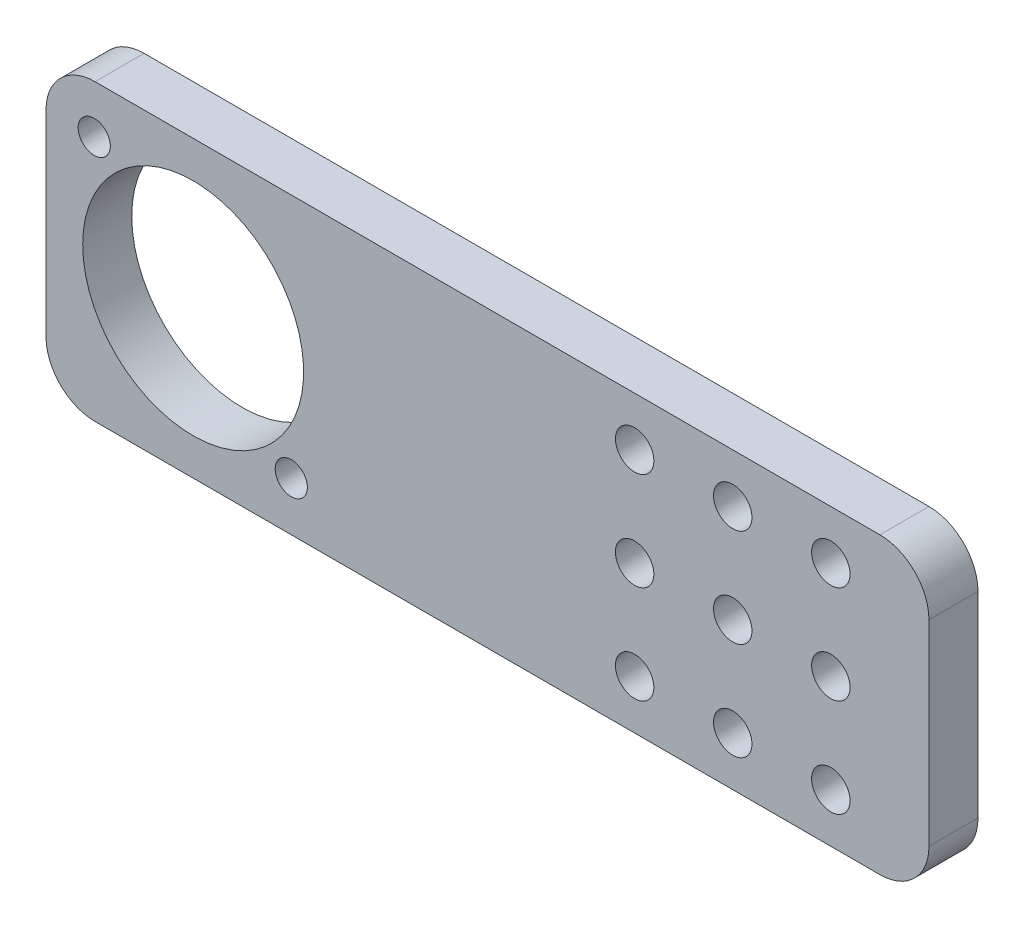
SolidWorks part; units mm, degrees
ref_plane "Front Plane" through (0, 0, 0) normal (0, 0, 1) x (1, 0, 0)
ref_plane "Top Plane" through (0, 0, 0) normal (0, 1, 0) x (1, 0, 0)
ref_plane "Right Plane" through (0, 0, 0) normal (1, 0, 0) x (0, 0, -1)
sketch "Sketch1" plane through (0, 0, 0) normal (0, 0, 1) x (1, 0, 0)
  line L0 (114.3, -12.7) -> (114.3, 12.7)
  line L1 (107.95, 19.05) -> (6.35, 19.05)
  line L2 (0, 12.7) -> (0, -12.7)
  line L3 (6.35, -19.05) -> (107.95, -19.05)
  line L4 (31.75, -12.7) -> (6.35, 12.7) construction
  circle A0 centre (19.05, 0) radius 14.3002
  circle A1 centre (6.2442, 12.8058) radius 2.0828
  circle A2 centre (31.75, -12.7) radius 2.0828
  circle A3 centre (88.9, 12.7) radius 2.4892
  circle A4 centre (101.6, 12.7) radius 2.4892
  circle A5 centre (88.9, 0) radius 2.4892
  circle A6 centre (101.6, 0) radius 2.4892
  circle A7 centre (88.9, -12.7) radius 2.4892
  circle A8 centre (76.2, 12.7) radius 2.4892
  circle A9 centre (101.6, -12.7) radius 2.4892
  circle A10 centre (76.2, 0) radius 2.4892
  circle A11 centre (76.2, -12.7) radius 2.4892
  arc A12 (107.95, -19.05) -> (114.3, -12.7) centre (107.95, -12.7) ccw
  arc A13 (114.3, 12.7) -> (107.95, 19.05) centre (107.95, 12.7) ccw
  arc A14 (6.35, 19.05) -> (0, 12.7) centre (6.35, 12.7) ccw
  arc A15 (0, -12.7) -> (6.35, -19.05) centre (6.35, -12.7) ccw
  point P6 (106.0367, -12.7)
  point P7 (0, 0)
  point P37 (0, 0)
  point P39 (88.9, 0)
  point P41 (19.05, 0)
  point P42 (114.3, 0)
  point P43 (114.3, 11.0389)
  point P44 (98.3474, 0)
  point P45 (114.3, 0)
  point P46 (101.6, 0)
  point P47 (103.7231, 0)
  point P48 (106.8631, 0)
  point P49 (93.3008, 0)
  point P50 (106.8368, 0)
  point P51 (106.8368, -13.9621)
  point P52 (97.8741, -12.1412)
  point P53 (65.4737, -4.9084)
  point P54 (88.9, -11.9742)
  point P55 (104.0892, 12.7)
  point P56 (38.7728, -2.3761)
  point P57 (0, 0)
  dimension "D6" = 4.1656
  dimension "D7" = 28.6004
  dimension "D8" = 6.35
  dimension "D9" = 4.9784
  dimension "D1" = 114.3
  dimension "D2" = 38.1
  dimension "D3" = 19.05
  dimension "D4" = 6.2442
  dimension "D5" = 6.2442
  dimension "D12" = 25.4
  dimension "D13" = 12.7
  dimension "D14" = 25.4
  dimension "D10" = 3
  dimension "D11" = 3
extrude "Boss-Extrude1" add sketch "Sketch1" against normal blind 6.35
